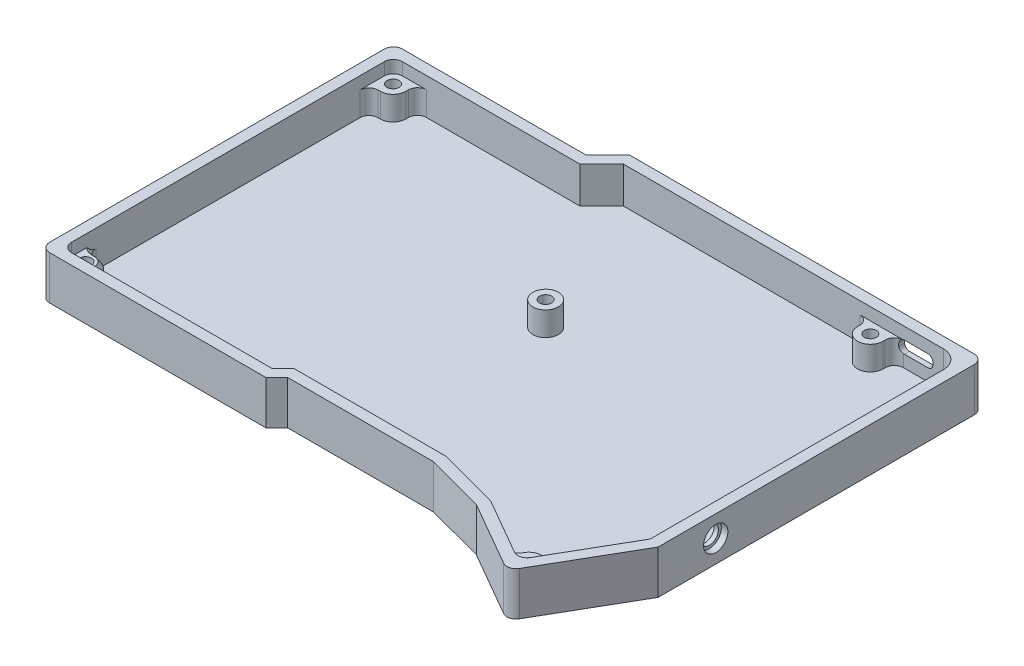
SolidWorks part; units mm, degrees
ref_plane "Front Plane" through (0, 0, 0) normal (0, 0, 1) x (1, 0, 0)
ref_plane "Top Plane" through (0, 0, 0) normal (0, 1, 0) x (1, 0, 0)
ref_plane "Right Plane" through (0, 0, 0) normal (1, 0, 0) x (0, 0, -1)
sketch "Sketch1" plane through (0, 0, 0) normal (0, 1, 0) x (1, 0, 0)
  line L0 (74.625, 48) -> (-17.625, 48) construction
  line L1 (-74.625, -48) -> (74.625, -48) construction
  line L2 (-74.625, -48) -> (-74.625, 48) construction
  line L3 (-74.625, 48) -> (74.625, 48) construction
  line L4 (74.625, -48) -> (74.625, 48) construction
  line L5 (-74.625, -48) -> (74.625, 48) construction
  line L6 (-74.625, 48) -> (74.625, -48) construction
  line L7 (-17.625, 48) -> (-17.625, 42) construction
  line L8 (-17.625, 42) -> (-23.625, 42) construction
  line L9 (-17.625, 48) -> (-23.625, 42) construction
  line L10 (-23.625, 42) -> (-74.625, 42) construction
  line L11 (-74.625, 42) -> (-74.625, -48) construction
  line L12 (-74.625, -48) -> (-17.625, -48) construction
  line L13 (-17.625, -48) -> (-17.625, -45) construction
  line L14 (-17.625, -45) -> (-14.625, -45) construction
  line L15 (-14.625, -45) -> (-17.625, -48) construction
  line L16 (-14.625, -45) -> (27.375, -45) construction
  line L17 (74.625, 48) -> (74.625, -37) construction
  line L18 (27.375, -45) -> (44.3045, -45) construction
  line L19 (44.3045, -45) -> (44.3045, -49.5167) construction
  line L20 (44.3045, -49.5167) -> (27.375, -45) construction
  line L21 (44.3045, -49.5167) -> (61.6269, -49.5167) construction
  line L22 (61.6269, -49.5167) -> (61.6269, -59.5048) construction
  line L23 (44.3045, -49.5167) -> (61.6269, -59.5048) construction
  line L24 (74.625, -37) -> (61.6269, -59.5048) construction
  line L25 (75.125, -37.134) -> (61.81, -60.1875)
  line L26 (44.1119, -49.9828) -> (61.81, -60.1875)
  line L27 (44.1119, -49.9828) -> (27.3094, -45.5)
  line L28 (-14.4179, -45.5) -> (27.3094, -45.5)
  line L29 (-14.4179, -45.5) -> (-17.4179, -48.5)
  line L30 (-75.125, -48.5) -> (-17.4179, -48.5)
  line L31 (-75.125, 42.5) -> (-75.125, -48.5)
  line L32 (-23.8321, 42.5) -> (-75.125, 42.5)
  line L33 (-17.8321, 48.5) -> (-23.8321, 42.5)
  line L34 (75.125, 48.5) -> (-17.8321, 48.5)
  line L35 (75.125, 48.5) -> (75.125, -37.134)
  line L36 (78.125, -37.9381) -> (62.9085, -64.2839)
  line L37 (42.9562, -52.7794) -> (62.9085, -64.2839)
  line L38 (42.9562, -52.7794) -> (26.9161, -48.5)
  line L39 (-13.1753, -48.5) -> (26.9161, -48.5)
  line L40 (-13.1753, -48.5) -> (-16.1753, -51.5)
  line L41 (-78.125, -51.5) -> (-16.1753, -51.5)
  line L42 (-78.125, 45.5) -> (-78.125, -51.5)
  line L43 (-25.0747, 45.5) -> (-78.125, 45.5)
  line L44 (-19.0747, 51.5) -> (-25.0747, 45.5)
  line L45 (78.125, 51.5) -> (-19.0747, 51.5)
  line L46 (78.125, 51.5) -> (78.125, -37.9381)
  point P0 (0, 0)
  dimension "D1" = 149.25
  dimension "D2" = 96
  dimension "D3" = 92.25
  dimension "D4" = 6
  dimension "D5" = 6
  dimension "D6" = 57
  dimension "D7" = 3
  dimension "D8" = 3
  dimension "D9" = 42
  dimension "D10" = 85
  dimension "D11" = 16.9295
  dimension "D12" = 4.5167
  dimension "D13" = 17.3224
  dimension "D14" = 9.9881
  dimension "D15" = 0.5
  dimension "D16" = 3
extrude "Boss-Extrude1" add sketch "Sketch1" along normal blind 10
sketch "Sketch2" plane through (0, 0, 0) normal (0, -1, 0) x (1, 0, 0)
  line L11 (78.125, -51.5) -> (78.125, 37.9381)
  line L12 (78.125, 37.9381) -> (62.9085, 64.2839)
  line L13 (62.9085, 64.2839) -> (42.9562, 52.7794)
  line L14 (42.9562, 52.7794) -> (26.9161, 48.5)
  line L15 (26.9161, 48.5) -> (-13.1753, 48.5)
  line L16 (-13.1753, 48.5) -> (-16.1753, 51.5)
  line L17 (-16.1753, 51.5) -> (-78.125, 51.5)
  line L18 (-78.125, 51.5) -> (-78.125, -45.5)
  line L19 (-78.125, -45.5) -> (-25.0747, -45.5)
  line L20 (-25.0747, -45.5) -> (-19.0747, -51.5)
  line L21 (-19.0747, -51.5) -> (78.125, -51.5)
  line L22 (78.125, -51.5) -> (78.125, 37.9381)
  line L23 (78.125, 37.9381) -> (62.9085, 64.2839)
  line L24 (62.9085, 64.2839) -> (42.9562, 52.7794)
  line L25 (42.9562, 52.7794) -> (26.9161, 48.5)
  line L26 (26.9161, 48.5) -> (-13.1753, 48.5)
  line L27 (-13.1753, 48.5) -> (-16.1753, 51.5)
  line L28 (-16.1753, 51.5) -> (-78.125, 51.5)
  line L29 (-78.125, 51.5) -> (-78.125, -45.5)
  line L30 (-78.125, -45.5) -> (-25.0747, -45.5)
  line L31 (-25.0747, -45.5) -> (-19.0747, -51.5)
  line L32 (-19.0747, -51.5) -> (78.125, -51.5)
  dimension "D1" = 0
extrude "Boss-Extrude2" add sketch "Sketch2" along normal blind 2
fillet "Fillet1" radius 2.5 3 edges at (-75.125, 5, 48.5) (61.81, 5, 60.1875) (-75.125, 5, -42.5)
fillet "Fillet2" radius 2.5 4 edges at (-78.125, 4, 51.5) (62.9085, 4, 64.2839) (78.125, 4, -51.5) (-78.125, 4, -45.5)
fillet "Fillet4" radius 5 1 edges at (75.125, 5, -48.5)
sketch "Sketch3" plane through (0, 0, 0) normal (0, 1, 0) x (1, 0, 0)
  line L0 (-68.5, 39.3) -> (-68.5, 42.5)
  line L1 (-72, 35.8) -> (-75.125, 35.8)
  line L2 (-72, -41.8) -> (-75.125, -41.8)
  line L3 (-68.5, -45.3) -> (-68.5, -48.5)
  line L4 (-75.125, -41.8) -> (-75.125, -46)
  line L5 (-72.625, -48.5) -> (-68.5, -48.5)
  line L6 (-70.5823, 42.5) -> (-68.5, 42.5)
  line L7 (-75.125, 35.8) -> (-75.125, 37.7238)
  line L8 (60.7118, -55.9182) -> (-24914.9904, -43371.2077) construction
  line L9 (61.0782, -56.2838) -> (43376.3677, -25031.986) construction
  line L10 (62.3933, -53.0019) -> (65.0679, -54.5467)
  line L11 (-75.125, 40) -> (-75.125, -46)
  line L12 (-72.625, -48.5) -> (-17.4179, -48.5)
  line L13 (-17.4179, -48.5) -> (-14.4179, -45.5)
  line L14 (-14.4179, -45.5) -> (27.3094, -45.5)
  line L15 (27.3094, -45.5) -> (44.1119, -49.9828)
  line L16 (44.1119, -49.9828) -> (59.6458, -58.9397)
  line L17 (63.0594, -58.0242) -> (75.125, -37.134)
  line L18 (75.125, -37.134) -> (75.125, 43.5)
  line L19 (70.125, 48.5) -> (-17.8321, 48.5)
  line L20 (-17.8321, 48.5) -> (-23.8321, 42.5)
  line L21 (-23.8321, 42.5) -> (-72.625, 42.5)
  line L22 (-75.125, 40) -> (-75.125, -46) construction
  line L23 (-72.625, -48.5) -> (-17.4179, -48.5) construction
  line L24 (-17.4179, -48.5) -> (-14.4179, -45.5) construction
  line L25 (-14.4179, -45.5) -> (27.3094, -45.5) construction
  line L26 (27.3094, -45.5) -> (44.1119, -49.9828) construction
  line L27 (44.1119, -49.9828) -> (59.6458, -58.9397) construction
  line L28 (63.0594, -58.0242) -> (75.125, -37.134) construction
  line L29 (75.125, -37.134) -> (75.125, 43.5) construction
  line L30 (70.125, 48.5) -> (-17.8321, 48.5) construction
  line L31 (-17.8321, 48.5) -> (-23.8321, 42.5) construction
  line L32 (-23.8321, 42.5) -> (-72.625, 42.5) construction
  line L33 (57.6129, -54.2857) -> (56.1063, -56.8987)
  line L34 (56.1063, -56.8987) -> (59.6458, -58.9397)
  line L35 (63.0594, -58.0242) -> (65.0679, -54.5467)
  line L36 (56.645, 45.4) -> (56.645, 48.5)
  line L37 (49.645, 48.5) -> (51.5202, 48.5)
  line L38 (49.645, 48.5) -> (49.645, 45.4)
  line L39 (57.6003, -57.7602) -> (56.1063, -56.8987)
  circle A0 centre (-72, 39.3) radius 3.5
  circle A1 centre (-72, -45.3) radius 3.5
  circle A2 centre (60.645, -56.034) radius 3.5
  circle A3 centre (53.145, 45.4) radius 3.5
  arc A4 (-75.125, -46) -> (-72.625, -48.5) centre (-72.625, -46) ccw
  arc A5 (59.6458, -58.9397) -> (63.0594, -58.0242) centre (60.8946, -56.7739) ccw
  arc A7 (-72.625, 42.5) -> (-75.125, 40) centre (-72.625, 40) ccw
  arc A8 (-75.125, -46) -> (-72.625, -48.5) centre (-72.625, -46) ccw
  arc A9 (59.6458, -58.9397) -> (63.0594, -58.0242) centre (60.8946, -56.7739) ccw
  arc A11 (-72.625, 42.5) -> (-75.125, 40) centre (-72.625, 40) ccw
  circle A12 centre (0.325, 8.92) radius 3.5
  arc A16 (75.125, 43.5) -> (70.125, 48.5) centre (70.125, 43.5) ccw
  arc A17 (75.125, 43.5) -> (70.125, 48.5) centre (70.125, 43.5) ccw
  point P35 (62.3933, -53.0019)
  point P39 (58.8967, -59.0661)
  point P43 (57.6129, -54.2857)
  point P53 (57.6003, -57.7602)
  line M22 (-75.125, 40) -> (-75.125, -46)
  arc M23 (-75.125, -46) -> (-72.625, -48.5) centre (-72.625, -46) ccw
  line M24 (-72.625, -48.5) -> (-17.4179, -48.5)
  line M28 (44.1119, -49.9828) -> (59.6458, -58.9397)
  arc M29 (59.6458, -58.9397) -> (63.0594, -58.0242) centre (60.8946, -56.7739) ccw
  line M30 (63.0594, -58.0242) -> (75.125, -37.134)
  line M33 (70.125, 48.5) -> (-17.8321, 48.5)
  line M35 (-23.8321, 42.5) -> (-72.625, 42.5)
  arc M36 (-72.625, 42.5) -> (-75.125, 40) centre (-72.625, 40) ccw
  dimension "D2" = 7
  dimension "D3" = 7
  dimension "D4" = 7
  dimension "D5" = 7
  dimension "D15" = 7
  dimension "D6" = 3.125
  dimension "D7" = 3.2
  dimension "D8" = 3.2
  dimension "D9" = 3.125
  dimension "D10" = 14.48
  dimension "D11" = 18.9
  dimension "D12" = 3.1
  dimension "D13" = 21.98
  dimension "D16" = 75.45
  dimension "D17" = 33.58
  dimension "D1" = 0
extrude "Boss-Extrude3" add sketch "Sketch3" along normal blind 6.6 contours A1 L4 M24 M23 | A1 L2 M22 | A0 L0 M35 | A0 M35 M36 M22 | A0 L1 M22 | A12 | A3 M33 | A3 L36 M33 | A3 L38 M33 | A2 L35 L10 | A2 L34 M30 M29 | A2 L33 M28 | A1 L5 L3
sketch "Sketch5" plane through (0, 6.6, 0) normal (0, 1, 0) x (1, 0, 0)
  arc A0 (49.645, 45.4) -> (56.645, 45.4) centre (53.145, 45.4) ccw construction
  arc A1 (62.3933, -53.0019) -> (57.6129, -54.2857) centre (60.645, -56.034) ccw construction
  arc A2 (-68.5, -45.3) -> (-72, -41.8) centre (-72, -45.3) ccw construction
  circle A3 centre (0.325, 8.92) radius 3.5 construction
  arc A4 (-72, 35.8) -> (-68.5, 39.3) centre (-72, 39.3) ccw construction
  arc A5 (49.645, 45.4) -> (56.645, 45.4) centre (53.145, 45.4) ccw construction
  arc A6 (62.3933, -53.0019) -> (57.6129, -54.2857) centre (60.645, -56.034) ccw construction
  arc A7 (-68.5, -45.3) -> (-72, -41.8) centre (-72, -45.3) ccw construction
  circle A8 centre (0.325, 8.92) radius 3.5 construction
  arc A9 (-72, 35.8) -> (-68.5, 39.3) centre (-72, 39.3) ccw construction
  circle A10 centre (-72, 39.3) radius 1.65
  circle A11 centre (0.325, 8.92) radius 1.65
  circle A12 centre (53.145, 45.4) radius 1.65
  circle A13 centre (60.645, -56.034) radius 1.65
  circle A14 centre (-72, -45.3) radius 1.65
  dimension "D1" = 3.3
  dimension "D2" = 3.3
  dimension "D3" = 3.3
  dimension "D4" = 3.3
  dimension "D5" = 3.3
extrude "Cut-Extrude1" cut sketch "Sketch5" against normal blind 2.5
fillet "Fillet3" radius 2.5 8 edges at (65.0679, 3.3, 54.5467) (49.645, 3.3, -48.5) (56.645, 3.3, -48.5) (-75.125, 3.3, -35.8) (-68.5, 3.3, -42.5) (-75.125, 3.3, 41.8) (56.1063, 3.3, 56.8987) (-68.5, 3.3, 48.5)
sketch "Sketch6" plane through (75.125, 0, 0) normal (-1, 0, 0) x (0, 0, 1)
  line L0 (37.134, 10) -> (37.134, 0) construction
  line L1 (37.134, 0) -> (-43.5, 0) construction
  circle A0 centre (22.0991, 4.1) radius 2.55
  dimension "D1" = 5.1
  dimension "D2" = 15.0349
  dimension "D3" = 4.1
extrude "Cut-Extrude2" cut sketch "Sketch6" against normal through all
sketch "Sketch7" plane through (78.125, 0, 0) normal (1, 0, 0) x (0, 0, -1)
  circle A0 centre (-22.0991, 4.1) radius 3.35
  dimension "D1" = 6.7
extrude "Cut-Extrude3" cut sketch "Sketch7" against normal blind 1.8
sketch "Sketch8" plane through (0, 0, -51.5) normal (0, 0, -1) x (-1, 0, 0)
  line L0 (-75.625, 10) -> (-75.625, -2) construction
  line L1 (-67.23, 3.34) -> (-58.09, 3.34)
  line L2 (-67.23, 3.34) -> (-67.23, 6.7)
  line L3 (-67.23, 6.7) -> (-58.09, 6.7)
  line L4 (-58.09, 3.34) -> (-58.09, 6.7)
  line L5 (-67.23, 3.34) -> (-58.09, 6.7) construction
  line L6 (-67.23, 6.7) -> (-58.09, 3.34) construction
  line L7 (19.0747, -2) -> (-75.625, -2) construction
  point P0 (-62.66, 5.02)
  dimension "D1" = 3.36
  dimension "D2" = 9.14
  dimension "D3" = 8.395
  dimension "D4" = 5.34
extrude "Cut-Extrude4" cut sketch "Sketch8" against normal up to next
fillet "Fillet5" radius 1.3 4 edges at (67.23, 3.34, -50) (58.09, 3.34, -49.8832) (58.09, 6.7, -50) (67.23, 6.7, -50)
sketch "Sketch9" plane through (0, 0, -51.5) normal (0, 0, -1) x (-1, 0, 0)
  line L0 (-67.23, 5.4) -> (-67.23, 4.64) construction
  line L1 (-65.93, 3.34) -> (-59.39, 3.34) construction
  line L2 (-58.09, 4.64) -> (-58.09, 5.4) construction
  line L3 (-59.39, 6.7) -> (-65.93, 6.7) construction
  line L4 (-67.23, 5.4) -> (-67.23, 4.64) construction
  line L5 (-65.93, 3.34) -> (-59.39, 3.34) construction
  line L6 (-58.09, 4.64) -> (-58.09, 5.4) construction
  line L7 (-59.39, 6.7) -> (-65.93, 6.7) construction
  line L8 (-69.73, 5.4) -> (-69.73, 4.64)
  line L9 (-65.93, 0.84) -> (-59.39, 0.84)
  line L10 (-55.59, 4.64) -> (-55.59, 5.4)
  line L11 (-59.39, 9.2) -> (-65.93, 9.2)
  arc A0 (-65.93, 6.7) -> (-67.23, 5.4) centre (-65.93, 5.4) ccw construction
  arc A1 (-67.23, 4.64) -> (-65.93, 3.34) centre (-65.93, 4.64) ccw construction
  arc A2 (-59.39, 3.34) -> (-58.09, 4.64) centre (-59.39, 4.64) ccw construction
  arc A3 (-58.09, 5.4) -> (-59.39, 6.7) centre (-59.39, 5.4) ccw construction
  arc A4 (-65.93, 6.7) -> (-67.23, 5.4) centre (-65.93, 5.4) ccw construction
  arc A5 (-67.23, 4.64) -> (-65.93, 3.34) centre (-65.93, 4.64) ccw construction
  arc A6 (-59.39, 3.34) -> (-58.09, 4.64) centre (-59.39, 4.64) ccw construction
  arc A7 (-58.09, 5.4) -> (-59.39, 6.7) centre (-59.39, 5.4) ccw construction
  arc A8 (-69.73, 4.64) -> (-65.93, 0.84) centre (-65.93, 4.64) ccw
  arc A9 (-59.39, 0.84) -> (-55.59, 4.64) centre (-59.39, 4.64) ccw
  arc A10 (-55.59, 5.4) -> (-59.39, 9.2) centre (-59.39, 5.4) ccw
  arc A11 (-65.93, 9.2) -> (-69.73, 5.4) centre (-65.93, 5.4) ccw
  dimension "D1" = 2.5
extrude "Cut-Extrude5" cut sketch "Sketch9" against normal blind 1.6 contours L8 A8 L9 A9 L10 A10 L11 A11
chamfer "Chamfer1" distance 1.5 angle 35 5 edges at (-67.7678, 6.6, 47.7678) (-74.3928, 6.6, 41.0678) (-68.5, 6.6, 45.65) (-72.3125, 6.6, 41.8) (-69.5251, 6.6, 42.8251)
equation "\"1.5.000000mm\"=10"
